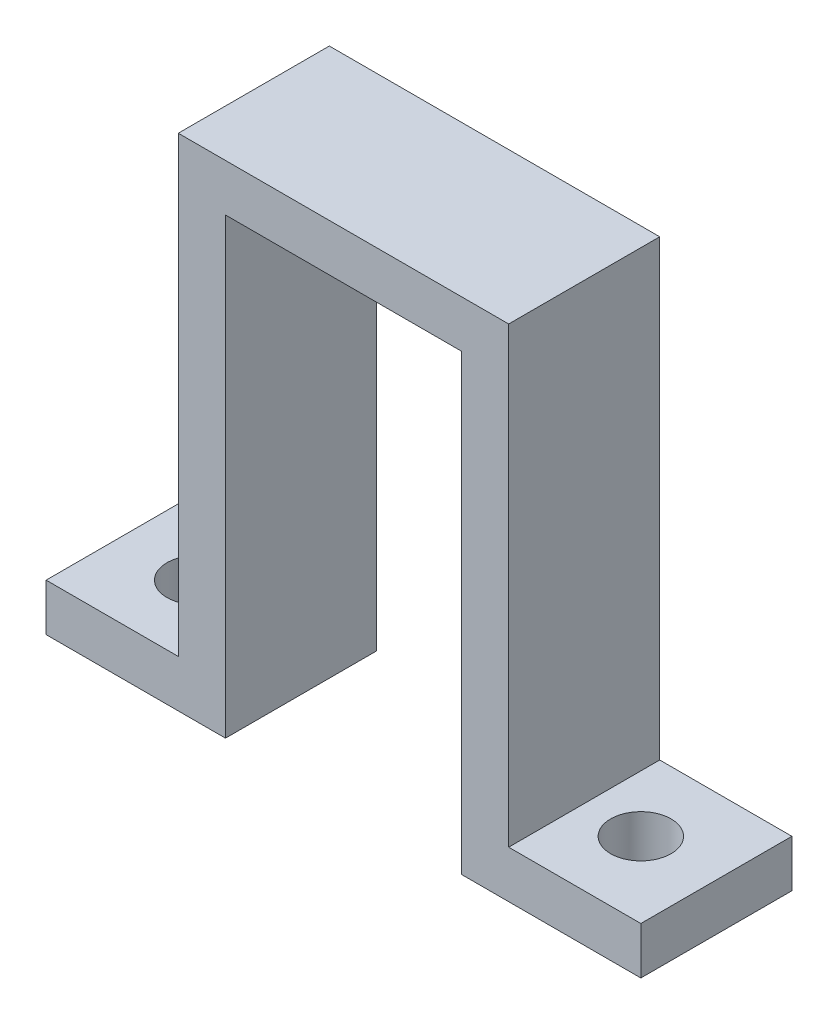
SolidWorks part; units mm, degrees
ref_plane "Front Plane" through (0, 0, 0) normal (0, 0, 1) x (1, 0, 0)
ref_plane "Top Plane" through (0, 0, 0) normal (0, 1, 0) x (1, 0, 0)
ref_plane "Right Plane" through (0, 0, 0) normal (1, 0, 0) x (0, 0, -1)
sketch "Sketch1" plane through (0, 0, 0) normal (0, 0, 1) x (1, 0, 0)
  line L0 (-6.1532, -0.6525) -> (-15.6532, -0.6525)
  line L1 (-15.6532, -0.6525) -> (-15.6532, 1.8475)
  line L2 (-15.6532, 1.8475) -> (-8.6532, 1.8475)
  line L3 (-8.6532, 1.8475) -> (-8.6532, 25.8475)
  line L4 (-8.6532, 25.8475) -> (8.8468, 25.8475)
  line L5 (8.8468, 25.8475) -> (8.8468, 1.8475)
  line L6 (8.8468, 1.8475) -> (15.8468, 1.8475)
  line L7 (15.8468, 1.8475) -> (15.8468, -0.6525)
  line L8 (15.8468, -0.6525) -> (6.3468, -0.6525)
  line L9 (6.3468, -0.6525) -> (6.3468, 23.3475)
  line L10 (6.3468, 23.3475) -> (-6.1532, 23.3475)
  line L11 (-6.1532, 23.3475) -> (-6.1532, -0.6525)
  dimension "D1" = 12.5
  dimension "D2" = 24
  dimension "D3" = 2.5
  dimension "D4" = 2.5
  dimension "D5" = 2.5
  dimension "D6" = 2.5
  dimension "D7" = 7
extrude "Boss-Extrude1" add sketch "Sketch1" along normal blind 8
sketch "Sketch2" plane through (0, 1.8475, 0) normal (0, 1, 0) x (1, 0, 0)
  line L0 (-12.1532, -8) -> (-12.1532, 0) construction
  line L1 (-8.6532, -8) -> (-15.6532, -8) construction
  line L2 (-8.6532, 0) -> (-15.6532, 0) construction
  line L3 (0.0968, -8) -> (0.0968, 3.6955) construction
  line L4 (8.8468, -8) -> (-8.6532, -8) construction
  circle A0 centre (-11.6532, -4) radius 1.6
  circle A1 centre (11.8468, -4) radius 1.6
  dimension "D1" = 3.2
  dimension "D2" = 23.5
extrude "Cut-Extrude1" cut sketch "Sketch2" against normal blind 10
equation "\"D4@Sketch1\"=\"D3@Sketch1\""
equation "\"D5@Sketch1\"=\"D3@Sketch1\""
equation "\"D6@Sketch1\"=\"D3@Sketch1\""
